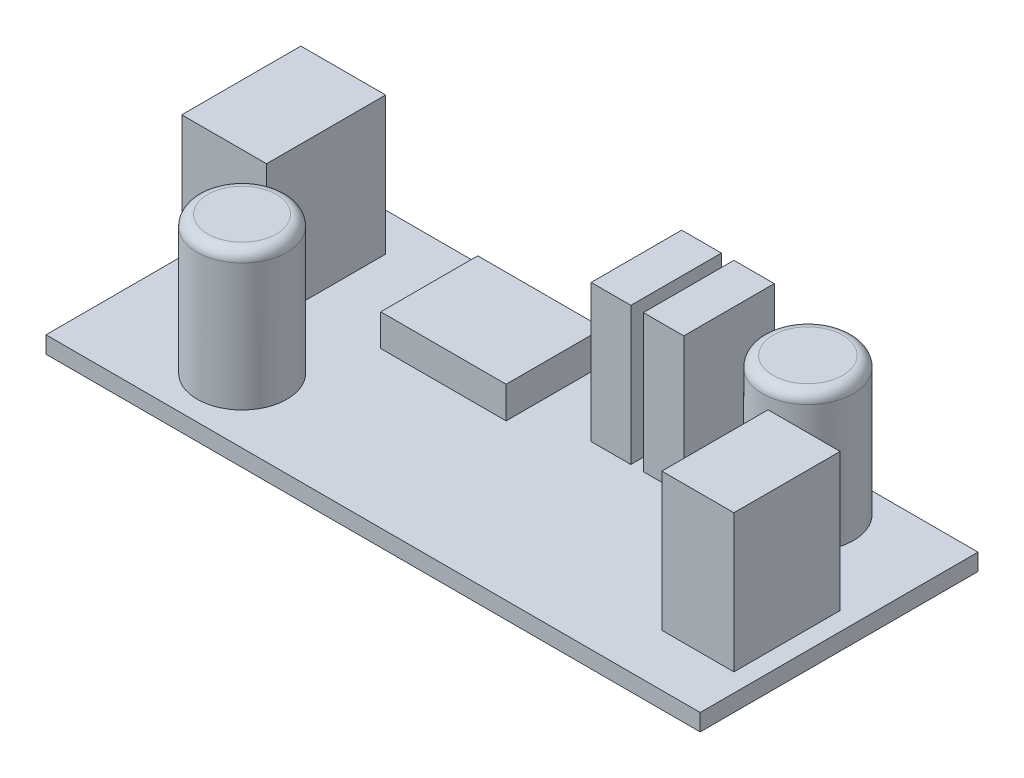
SolidWorks part; units mm, degrees
ref_plane "Front Plane" through (0, 0, 0) normal (0, 0, 1) x (1, 0, 0)
ref_plane "Top Plane" through (0, 0, 0) normal (0, 1, 0) x (1, 0, 0)
ref_plane "Right Plane" through (0, 0, 0) normal (1, 0, 0) x (0, 0, -1)
sketch "Sketch1" plane through (0, 0, 0) normal (0, 1, 0) x (1, 0, 0)
  line L1 (0, 0) -> (61.7, 0)
  line L2 (0, 0) -> (0, 26.2)
  line L3 (0, 26.2) -> (61.7, 26.2)
  line L4 (61.7, 0) -> (61.7, 26.2)
  dimension "D1" = 26.2
  dimension "D2" = 61.7
extrude "Boss-Extrude1" add sketch "Sketch1" along normal blind 1.59
sketch "Sketch2" plane through (0, 1.59, 0) normal (0, 1, 0) x (1, 0, 0)
  line L1 (1.4332, 22.6025) -> (9.4295, 22.6025)
  line L2 (1.4332, 22.6025) -> (1.4332, 11.3709)
  line L3 (1.4332, 11.3709) -> (9.4295, 11.3709)
  line L4 (9.4295, 22.6025) -> (9.4295, 11.3709)
  line L5 (53.1758, 14.9218) -> (59.9732, 14.9218)
  line L6 (53.1758, 14.9218) -> (53.1758, 4.9064)
  line L7 (53.1758, 4.9064) -> (59.9732, 4.9064)
  line L8 (59.9732, 14.9218) -> (59.9732, 4.9064)
  line L9 (34.4293, 25.5244) -> (38.1737, 25.5244)
  line L10 (34.4293, 25.5244) -> (34.4293, 16.9867)
  line L11 (34.4293, 16.9867) -> (38.1737, 16.9867)
  line L12 (38.1737, 25.5244) -> (38.1737, 16.9867)
  line L13 (39.3579, 25.5244) -> (43.1627, 25.5244)
  line L14 (39.3579, 25.5244) -> (39.3579, 16.9867)
  line L15 (39.3579, 16.9867) -> (43.1627, 16.9867)
  line L16 (43.1627, 25.5244) -> (43.1627, 16.9867)
  circle A0 centre (50.6012, 21.2556) radius 4.2842
  circle A1 centre (12.3986, 6.0957) radius 4.2335
extrude "Boss-Extrude2" add sketch "Sketch2" along normal blind 13
fillet "Fillet1" radius 1 2 edges at (50.6012, 14.59, -16.9713) (12.3986, 14.59, -1.8622)
sketch "Sketch3" plane through (0, 1.59, 0) normal (0, 1, 0) x (1, 0, 0)
  line L1 (16.9089, 23.8112) -> (28.7337, 23.8112)
  line L2 (16.9089, 23.8112) -> (16.9089, 14.6618)
  line L3 (16.9089, 14.6618) -> (28.7337, 14.6618)
  line L4 (28.7337, 23.8112) -> (28.7337, 14.6618)
extrude "Boss-Extrude3" add sketch "Sketch3" along normal blind 3
